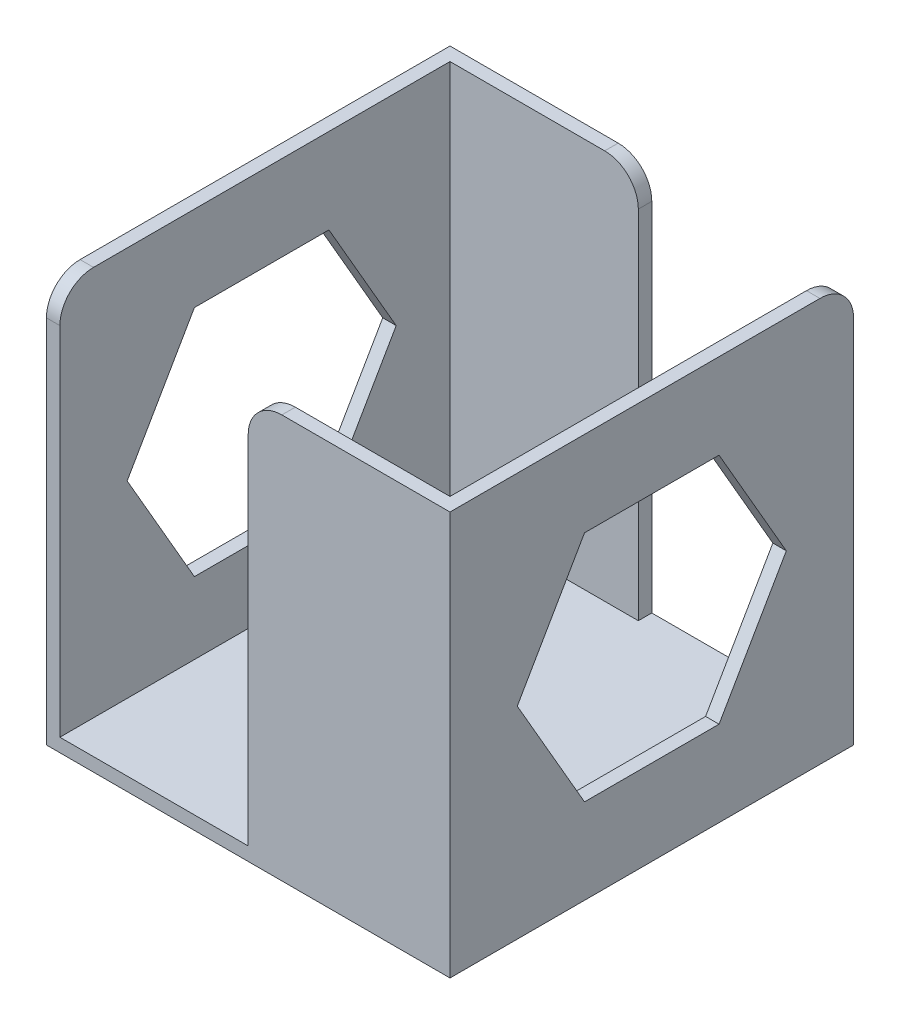
SolidWorks part; units mm, degrees
ref_plane "Front Plane" through (0, 0, 0) normal (0, 0, 1) x (1, 0, 0)
ref_plane "Top Plane" through (0, 0, 0) normal (0, 1, 0) x (1, 0, 0)
ref_plane "Right Plane" through (0, 0, 0) normal (1, 0, 0) x (0, 0, -1)
sketch "Sketch1" plane through (0, 0, 0) normal (0, 1, 0) x (1, 0, 0)
  line L1 (-30, 30) -> (30, 30)
  line L2 (-30, 30) -> (-30, -30)
  line L3 (-30, -30) -> (30, -30)
  line L4 (30, 30) -> (30, -30)
  line L5 (-30, 30) -> (30, -30) construction
  line L6 (-30, -30) -> (30, 30) construction
  point P0 (0, 0)
  dimension "D1" = 60
extrude "Cube" add sketch "Sketch1" along normal blind 60
shell "Shell1" thickness 2
sketch "Sketch2" plane through (0, 0, 30) normal (0, 0, 1) x (1, 0, 0)
  line L0 (-28, 2) -> (28, 2) construction
  line L1 (-28, 60) -> (0, 60)
  line L2 (-28, 60) -> (-28, 2)
  line L3 (-28, 2) -> (0, 2)
  line L4 (0, 60) -> (0, 2)
extrude "Cut Out Left" cut sketch "Sketch2" against normal up to surface (2 mm away) up to face at (0, 31, 28)
sketch "Sketch3" plane through (0, 0, -30) normal (0, 0, -1) x (-1, 0, 0)
  line L0 (-30, 60) -> (30, 60) construction
  line L1 (-28, 2) -> (0, 2)
  line L2 (-28, 2) -> (-28, 60)
  line L3 (-28, 60) -> (0, 60)
  line L4 (0, 2) -> (0, 60)
extrude "Cut Out Right" cut sketch "Sketch3" against normal up to next
sketch "Sketch4" plane through (30, 0, 0) normal (1, 0, 0) x (0, 0, -1)
  line L0 (-30, 60) -> (30, 0) construction
  line L2 (20, 30) -> (10, 47.3205)
  line L3 (10, 47.3205) -> (-10, 47.3205)
  line L4 (-10, 47.3205) -> (-20, 30)
  line L5 (-20, 30) -> (-10, 12.6795)
  line L6 (-10, 12.6795) -> (10, 12.6795)
  line L7 (10, 12.6795) -> (20, 30)
  circle A0 centre (0, 30) radius 17.3205 construction
  dimension "D1" = 20
extrude "Hex Cut" cut sketch "Sketch4" against normal through all
fillet "Fillet1" radius 5 4 edges at (29, 60, -30) (0, 60, -29) (0, 60, 29) (-29, 60, 30)
